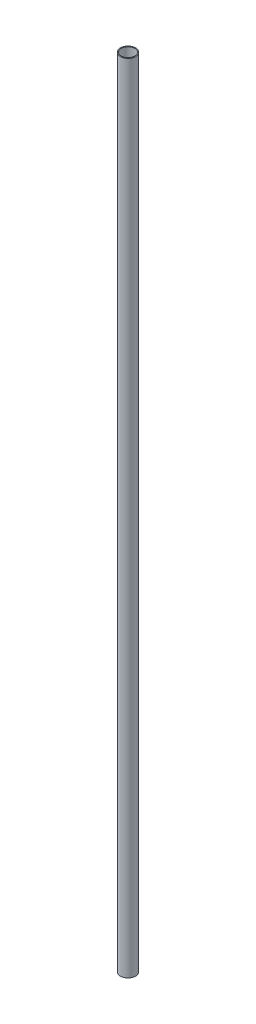
SolidWorks part; units mm, degrees
material "Galvanized Steel"
ref_plane "Front Plane" through (0, 0, 0) normal (0, 0, 1) x (1, 0, 0)
ref_plane "Top Plane" through (0, 0, 0) normal (0, 1, 0) x (1, 0, 0)
ref_plane "Right Plane" through (0, 0, 0) normal (1, 0, 0) x (0, 0, -1)
sketch "Sketch1" plane through (0, 0, 0) normal (0, 1, 0) x (1, 0, 0)
  circle A0 centre (0, 0) radius 8.9662
  circle A1 centre (0, 0) radius 7.8994
  dimension "D1" = 17.9324
  dimension "D2" = 15.7988
extrude "Boss-Extrude1" add sketch "Sketch1" against normal blind 939.8
